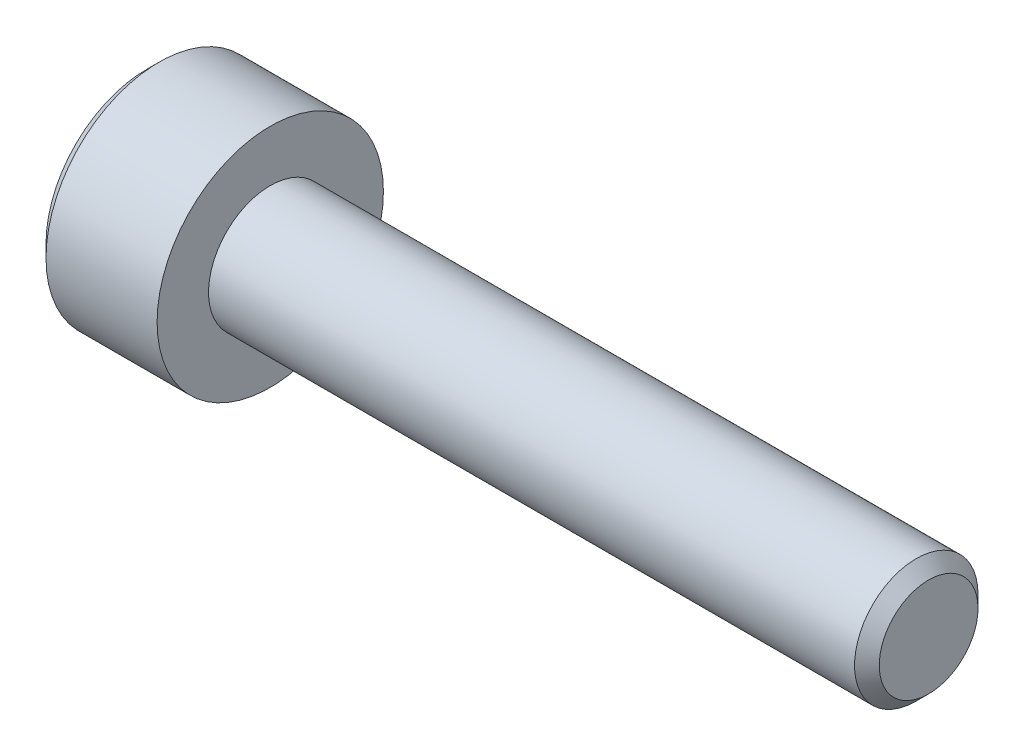
SolidWorks part; units mm, degrees
ref_plane "前视基准面" through (0, 0, 0) normal (0, 0, 1) x (1, 0, 0)
ref_plane "上视基准面" through (0, 0, 0) normal (0, 1, 0) x (1, 0, 0)
ref_plane "右视基准面" through (0, 0, 0) normal (1, 0, 0) x (0, 0, -1)
ref_plane "基准面1" through (0, 0, 0) normal (0, 0, -1) x (-1, 0, 0)
sketch "草图1" plane through (0, 0, 0) normal (0, 0, -1) x (-1, 0, 0)
  line L0 (-3, 2.75) -> (-3, 0)
  line L1 (-3, 0) -> (0, 0)
  line L2 (0, 0) -> (0, 2.75)
  line L3 (0, 2.75) -> (-3, 2.75)
  line L4 (-3, 0) -> (0, 0) construction
revolve "旋转1" add sketch "草图1" angle 360 about L4
sketch "草图2" plane through (3, 0, 0) normal (1, 0, 0) x (0, 0, -1)
  circle A0 centre (0, 0) radius 1.5
extrude "凸台-拉伸1" add sketch "草图2" along normal blind 16
sketch "草图3" plane through (0, 0, 0) normal (-1, 0, 0) x (0, 0, 1)
  line L0 (1.28, 0.739) -> (0, 1.478)
  line L1 (0, 1.478) -> (-1.28, 0.739)
  line L2 (-1.28, 0.739) -> (-1.28, -0.739)
  line L3 (-1.28, -0.739) -> (0, -1.478)
  line L4 (0, -1.478) -> (1.28, -0.739)
  line L5 (1.28, -0.739) -> (1.28, 0.739)
extrude "切除-拉伸1" cut sketch "草图3" against normal blind 1.3
sketch "草图4" plane through (0, 0, 0) normal (0, 0, 1) x (1, 0, 0)
  line L0 (1.3, 1.28) -> (1.3, 0)
  line L1 (1.3, 0) -> (2.039, 0)
  line L2 (2.039, 0) -> (1.3, 1.28)
  line L3 (1.3, 0) -> (2.039, 0) construction
revolve "切除-旋转1" cut sketch "草图4" angle 360 about L3
chamfer "倒角1" distance 0.3 angle 45 2 edges at (19, 0, -1.5) (0, 0, 2.75)
